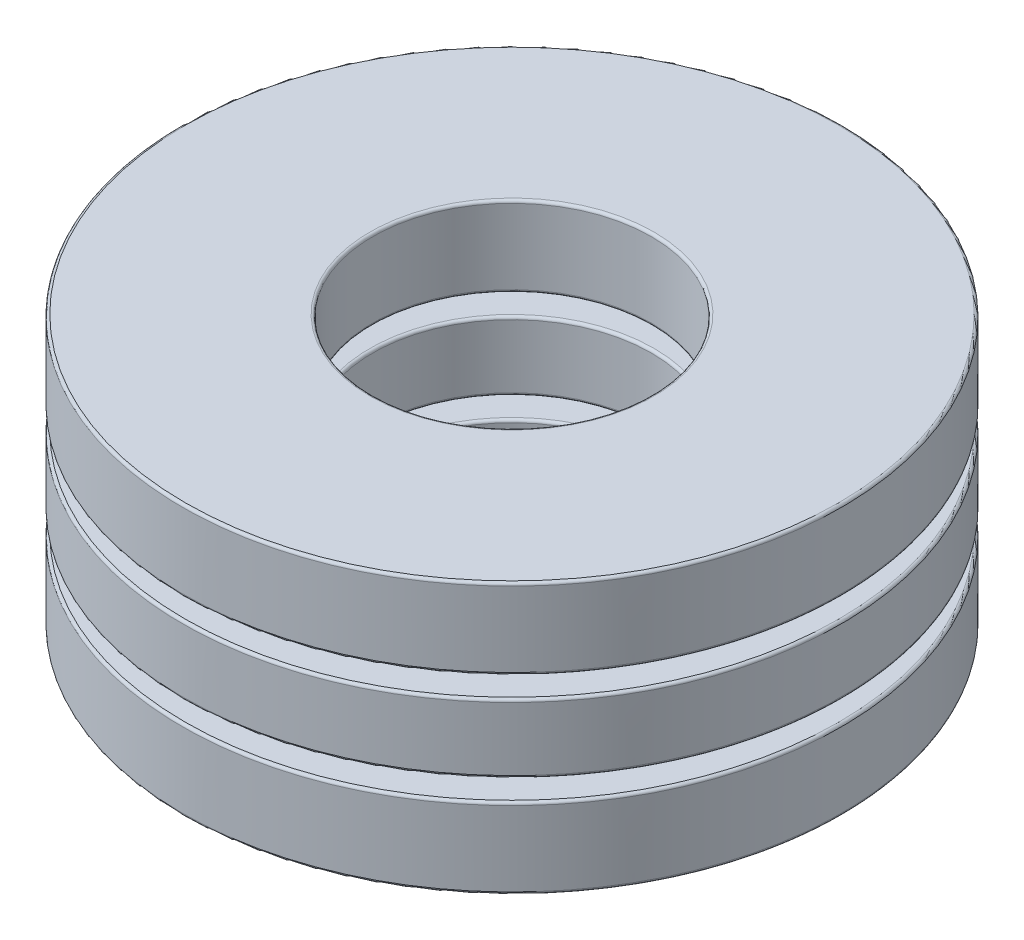
SolidWorks part; units mm, degrees
ref_plane "Front Plane" through (0, 0, 0) normal (0, 0, 1) x (1, 0, 0)
ref_plane "Top Plane" through (0, 0, 0) normal (0, 1, 0) x (1, 0, 0)
ref_plane "Right Plane" through (0, 0, 0) normal (1, 0, 0) x (0, 0, -1)
sketch "Sketch1" plane through (0, 0, 0) normal (1, 0, 0) x (0, 0, -1)
  line L0 (-6, 0) -> (6, 0) construction
  line L1 (0, -2.46) -> (0, 2.46) construction
  line L2 (-6, 0.625) -> (-2.538, 0.625)
  line L3 (-6, 0.625) -> (-6, -0.625)
  line L4 (-6, -0.625) -> (-2.538, -0.625)
  line L5 (-2.538, 0.625) -> (-2.538, -0.625)
  line L6 (-4.5, 1) -> (-4.5, -1) construction
  circle A0 centre (-4.5, 0) radius 1 construction
  dimension "D2" = 1.25
revolve "Revolve1" add sketch "Sketch1" angle 360 about L1
sketch "Sketch3" plane through (0, 0, 0) normal (1, 0, 0) x (0, 0, -1)
  line L0 (-4.5, 1.0625) -> (-4.5, -1.0625)
  line L1 (-4.5, 1) -> (-4.5, -1) construction
  line L2 (-4.4375, 1.0607) -> (-4.4375, -1.0607) construction
  arc A0 (-4.5, 1) -> (-4.5, -1) centre (-4.5, 0) ccw construction
  circle A1 centre (-4.5, 0) radius 1 construction
  arc A2 (-4.5, 1.0625) -> (-4.5, -1.0625) centre (-4.5, 0) ccw
  arc A3 (-4.4375, 1.0607) -> (-4.4375, -1.0607) centre (-4.5, 0) ccw construction
  dimension "D1" = 0.0625
revolve "Cut-Revolve1" cut sketch "Sketch3" angle 360 about L0
sketch "Sketch2" plane through (0, 0, 0) normal (1, 0, 0) x (0, 0, -1)
  line L0 (-4.5, 1) -> (-4.5, -1)
  arc A0 (-4.5, 1) -> (-4.5, -1) centre (-4.5, 0) ccw
  circle A2 centre (-4.5, 0) radius 1 construction
revolve "Revolve2" add sketch "Sketch2" angle 360 about L0
ref_axis "Axis1" through (0, 2.46, 0) along (0, -1, 0)
pattern_circular "CirPattern1" count 7 every 51.429 about axis through (0, 2.46, 0) along (0, -1, 0) of bodies 187
pattern_circular "CirPattern2" count 7 every 51.429 about axis through (0, 0, 0) along (0, 1, 0) of "Cut-Revolve1"
sketch "Sketch4" plane through (0, 0, 0) normal (1, 0, 0) x (0, 0, -1)
  line L0 (-6, 0.625) -> (-6, -0.625) construction
  line L1 (-6, 1) -> (-2.538, 1)
  line L2 (-6, 1) -> (-6, 2.46)
  line L3 (-6, 2.46) -> (-2.538, 2.46)
  line L4 (-2.538, 1) -> (-2.538, 2.46)
  line L5 (-6, -2.46) -> (-2.538, -2.46)
  line L6 (-6, -2.46) -> (-6, -1)
  line L7 (-6, -1) -> (-2.538, -1)
  line L8 (-2.538, -2.46) -> (-2.538, -1)
  line L10 (-2.538, 0.625) -> (-2.538, -0.625) construction
  line L11 (0, 0) -> (-6, 0) construction
  line L12 (-6, 0) -> (6, 0) construction
  dimension "Ht" = 4.92
  dimension "Washer Thickness" = 1.46
revolve "Revolve3" add sketch "Sketch4" angle 360 about L1
fillet "Fillet1" radius 0.0492 4 edges at (0, 1, -2.538) (0, 2.46, -2.538) (0, 1, -6) (0, 2.46, -6)
fillet "Fillet2" radius 0.0492 4 edges at (0, -0.625, -2.538) (0, 0.625, -2.538) (0, -0.625, -6) (0, 0.625, -6)
fillet "Fillet3" radius 0.0492 4 edges at (0, -2.46, -2.538) (0, -1, -2.538) (0, -2.46, -6) (0, -1, -6)
equation "\"D2@Sketch1\" = \"Roller Ball Dia@Sketch1\"*.625"
equation "\"Angle@CirPattern1\" = 360/\"Balls@CirPattern1\""
equation "\"D1@CirPattern2\" = \"Balls@CirPattern1\""
equation "\"D2@CirPattern2\" = \"Angle@CirPattern1\""
equation "\"D1@Fillet1\" = \"Th@Sketch1\"*.01"
equation "\"D1@Fillet2\" = \"D1@Fillet1\""
equation "\"D1@Fillet3\" = \"D1@Fillet1\""
